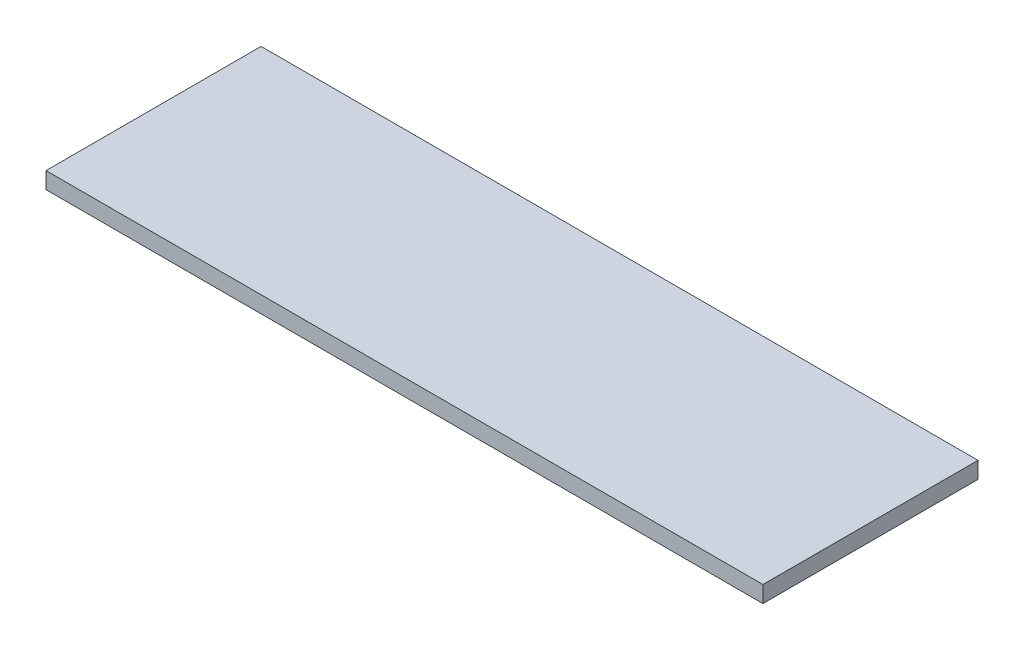
SolidWorks part; units mm, degrees
ref_plane "Front Plane" through (0, 0, 0) normal (0, 0, 1) x (1, 0, 0)
ref_plane "Top Plane" through (0, 0, 0) normal (0, 1, 0) x (1, 0, 0)
ref_plane "Right Plane" through (0, 0, 0) normal (1, 0, 0) x (0, 0, -1)
sketch "Sketch1" plane through (0, 0, 0) normal (0, 1, 0) x (1, 0, 0)
  line L1 (0, -2.8892) -> (130, -2.8892)
  line L2 (0, -2.8892) -> (0, 36.1108)
  line L3 (0, 36.1108) -> (130, 36.1108)
  line L4 (130, -2.8892) -> (130, 36.1108)
  dimension "D1" = 39
  dimension "D2" = 130
extrude "Boss-Extrude1" add sketch "Sketch1" along normal blind 3
